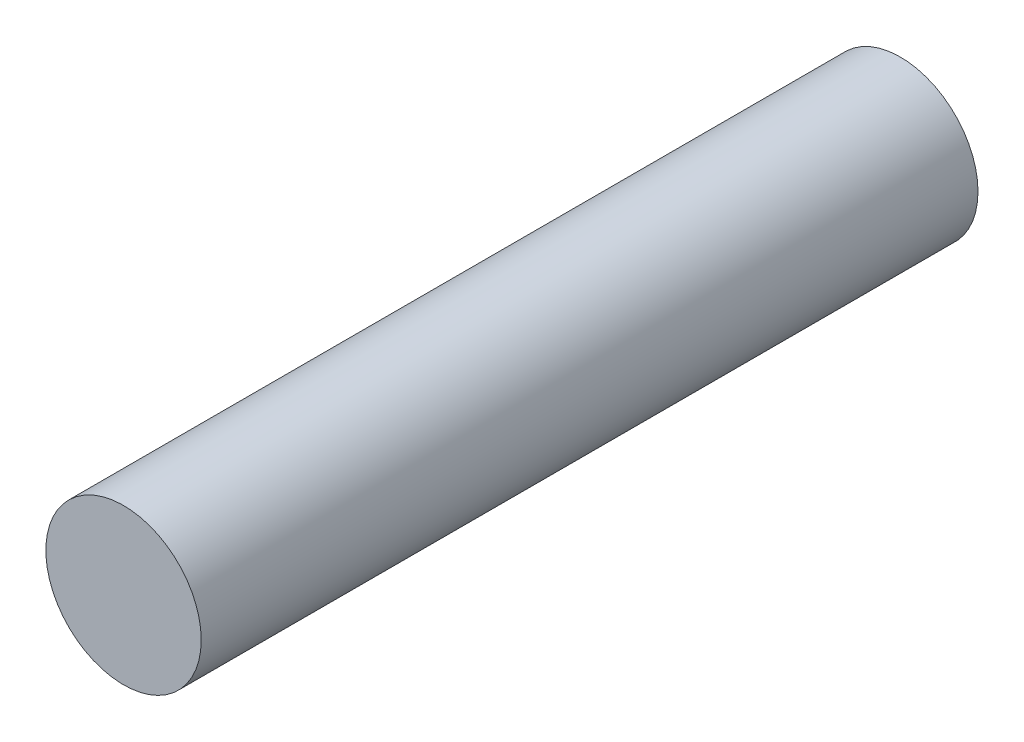
SolidWorks part; units mm, degrees
ref_plane "Front Plane" through (0, 0, 0) normal (0, 0, 1) x (1, 0, 0)
ref_plane "Top Plane" through (0, 0, 0) normal (0, 1, 0) x (1, 0, 0)
ref_plane "Right Plane" through (0, 0, 0) normal (1, 0, 0) x (0, 0, -1)
sketch "Sketch1" plane through (0, 0, 0) normal (0, 0, 1) x (1, 0, 0)
  circle A0 centre (0, 0) radius 3
extrude "Boss-Extrude1" add sketch "Sketch1" along normal blind 30
